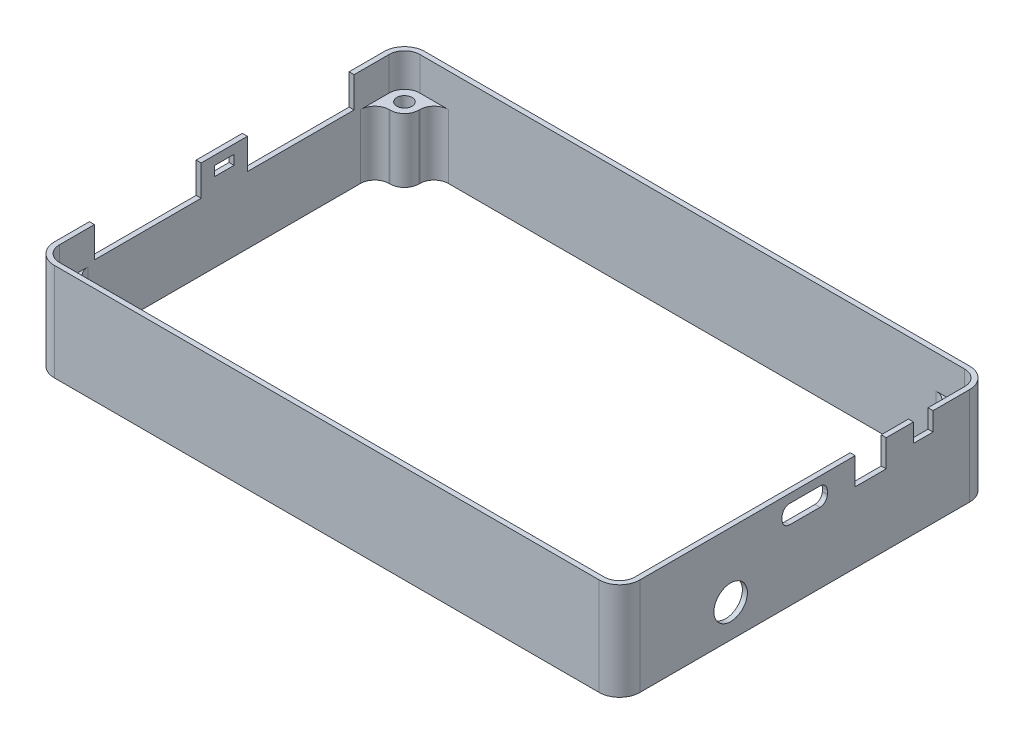
SolidWorks part; units mm, degrees
ref_plane "Front Plane" through (0, 0, 0) normal (0, 0, 1) x (1, 0, 0)
ref_plane "Top Plane" through (0, 0, 0) normal (0, 1, 0) x (1, 0, 0)
ref_plane "Right Plane" through (0, 0, 0) normal (1, 0, 0) x (0, 0, -1)
sketch "pcb" plane through (0, 0, 0) normal (0, 1, 0) x (1, 0, 0)
  line L0 (-14, -27.5) -> (-42, -27.5) construction
  line L1 (-57, -37.5) -> (57, -37.5)
  line L2 (-60, -34.5) -> (-60, 34.5)
  line L3 (-57, 37.5) -> (57, 37.5)
  line L4 (60, -34.5) -> (60, 34.5)
  line L5 (-60, -37.5) -> (60, 37.5) construction
  line L6 (-60, 37.5) -> (60, -37.5) construction
  line L7 (-14, -27.5) -> (14, -27.5) construction
  line L8 (14, -27.5) -> (42, -27.5) construction
  line L9 (-42, -27.5) -> (-60, -27.5) construction
  line L10 (42, -27.5) -> (60, -27.5) construction
  line L11 (-60, 0) -> (60, 0) construction
  line L13 (2.43, 12.5075) -> (10.05, 12.5075)
  line L14 (2.43, 12.5075) -> (2.43, 9.9675)
  line L15 (2.43, 9.9675) -> (10.05, 9.9675)
  line L16 (10.05, 12.5075) -> (10.05, 9.9675)
  arc A0 (-57, -37.5) -> (-60, -34.5) centre (-57, -34.5) cw
  arc A1 (57, -37.5) -> (60, -34.5) centre (57, -34.5) ccw
  arc A2 (57, 37.5) -> (60, 34.5) centre (57, 34.5) cw
  arc A3 (-60, 34.5) -> (-57, 37.5) centre (-57, 34.5) cw
  circle A4 centre (-57, 34.5) radius 1.6
  circle A5 centre (57, 34.5) radius 1.6
  circle A6 centre (57, -34.5) radius 1.6
  circle A7 centre (-57, -34.5) radius 1.6
  circle A8 centre (-42, -27.5) radius 5.5
  circle A9 centre (-14, -27.5) radius 5.5
  circle A10 centre (14, -27.5) radius 5.5
  circle A11 centre (42, -27.5) radius 5.5
  circle A12 centre (-42, 27.5) radius 5.5
  circle A13 centre (-14, 27.5) radius 5.5
  circle A14 centre (14, 27.5) radius 5.5
  circle A15 centre (42, 27.5) radius 5.5
  point P0 (0, 0)
  dimension "D3" = 3
  dimension "D4" = 3
  dimension "D5" = 3
  dimension "D6" = 3
  dimension "D7" = 3.2
  dimension "D9" = 11
  dimension "D10" = 18
  dimension "D1" = 120
  dimension "D2" = 75
  dimension "D8" = 10
  dimension "D11" = 62.43
  dimension "D12" = 47.4675
  dimension "D13" = 2.54
  dimension "D14" = 7.62
sketch "Sketch3" plane through (0, 0, 0) normal (0, 0, 1) x (1, 0, 0)
  line L0 (0, 0) -> (0, 1.6) construction
  line L1 (-57, 0) -> (57, 0) construction
  line L2 (0, 1.6) -> (0, 7) construction
  line L3 (0, 7) -> (0, 8.6) construction
  line L4 (0, 0) -> (0, -13.4) construction
  line L5 (0, -13.4) -> (0, -16.4) construction
  dimension "D1" = 1.6
  dimension "D2" = 3
  dimension "D3" = 13.4
  dimension "D4" = 5.4
  dimension "D5" = 1.6
  dimension "D6" = 25
sketch "Sketch2" plane through (0, 0, 0) normal (0, 1, 0) x (1, 0, 0)
  line L0 (-60, -34.5) -> (-60, 34.5) construction
  line L1 (-57, -37.5) -> (57, -37.5) construction
  line L2 (60, -34.5) -> (60, 34.5) construction
  line L3 (-57, 37.5) -> (57, 37.5) construction
  line L4 (-60, -34.5) -> (-60, 34.5)
  line L5 (-57, -37.5) -> (57, -37.5)
  line L6 (60, -34.5) -> (60, 34.5)
  line L7 (-57, 37.5) -> (57, 37.5)
  line L8 (-61.25, -34.5) -> (-61.25, 34.5)
  line L9 (-57, -38.75) -> (57, -38.75)
  line L10 (61.25, -34.5) -> (61.25, 34.5)
  line L11 (-57, 38.75) -> (57, 38.75)
  arc A0 (-57, 37.5) -> (-60, 34.5) centre (-57, 34.5) ccw construction
  arc A1 (-60, -34.5) -> (-57, -37.5) centre (-57, -34.5) ccw construction
  arc A2 (57, -37.5) -> (60, -34.5) centre (57, -34.5) ccw construction
  arc A3 (60, 34.5) -> (57, 37.5) centre (57, 34.5) ccw construction
  arc A4 (-57, 37.5) -> (-60, 34.5) centre (-57, 34.5) ccw
  arc A5 (-60, -34.5) -> (-57, -37.5) centre (-57, -34.5) ccw
  arc A6 (57, -37.5) -> (60, -34.5) centre (57, -34.5) ccw
  arc A7 (60, 34.5) -> (57, 37.5) centre (57, 34.5) ccw
  arc A8 (-57, 38.75) -> (-61.25, 34.5) centre (-57, 34.5) ccw
  arc A9 (-61.25, -34.5) -> (-57, -38.75) centre (-57, -34.5) ccw
  arc A10 (57, -38.75) -> (61.25, -34.5) centre (57, -34.5) ccw
  arc A11 (61.25, 34.5) -> (57, 38.75) centre (57, 34.5) ccw
  dimension "D1" = 1.25
extrude "Walls" add sketch "Sketch2" against normal up to vertex (13.4 mm away) and the other way up to vertex (7 mm away) up to point (0, -13.4, 0) other way up to point (0, 7, 0)
sketch "Sketch11" plane through (0, 0, 0) normal (0, 1, 0) x (1, 0, 0)
  line L0 (-60, -34.5) -> (-60, -31.5)
  line L1 (-60, -34.5) -> (-60, 34.5) construction
  line L2 (-60, -31.5) -> (-54, -31.5)
  line L3 (-54, -31.5) -> (-54, -37.5)
  line L4 (-57, -37.5) -> (57, -37.5) construction
  line L5 (-54, -37.5) -> (-57, -37.5)
  line L6 (-57, 37.5) -> (-54, 37.5)
  line L7 (-57, 37.5) -> (57, 37.5) construction
  line L8 (-54, 37.5) -> (-54, 31.5)
  line L9 (-54, 31.5) -> (-60, 31.5)
  line L10 (-60, 31.5) -> (-60, 34.5)
  line L11 (60, -31.5) -> (54, -31.5)
  line L12 (60, -34.5) -> (60, 34.5) construction
  line L13 (54, -31.5) -> (54, -37.5)
  line L14 (54, -37.5) -> (57, -37.5)
  line L15 (60, -31.5) -> (60, -34.5)
  line L16 (57, 37.5) -> (54, 37.5)
  line L17 (54, 37.5) -> (54, 31.5)
  line L18 (54, 31.5) -> (60, 31.5)
  line L19 (60, 31.5) -> (60, 34.5)
  arc A0 (-60, -34.5) -> (-57, -37.5) centre (-57, -34.5) ccw construction
  arc A1 (-60, -34.5) -> (-57, -37.5) centre (-57, -34.5) ccw
  arc A2 (-57, 37.5) -> (-60, 34.5) centre (-57, 34.5) ccw construction
  arc A3 (-57, 37.5) -> (-60, 34.5) centre (-57, 34.5) ccw
  circle A4 centre (-57, 34.5) radius 1.6 construction
  circle A5 centre (-57, 34.5) radius 1.6
  circle A6 centre (-57, -34.5) radius 1.6 construction
  circle A7 centre (-57, -34.5) radius 1.6
  arc A8 (57, -37.5) -> (60, -34.5) centre (57, -34.5) ccw construction
  arc A9 (57, -37.5) -> (60, -34.5) centre (57, -34.5) ccw
  circle A10 centre (57, -34.5) radius 1.6 construction
  circle A11 centre (57, -34.5) radius 1.6
  arc A12 (60, 34.5) -> (57, 37.5) centre (57, 34.5) ccw construction
  arc A13 (60, 34.5) -> (57, 37.5) centre (57, 34.5) ccw
  circle A14 centre (57, 34.5) radius 1.6 construction
  circle A15 centre (57, 34.5) radius 1.6
  dimension "D1" = 6
  dimension "D2" = 6
  dimension "D3" = 6
  dimension "D4" = 6
extrude "Boss-Extrude4" add sketch "Sketch11" against normal up to surface (13.4 mm away) up to face at (0, -13.4, 0)
other "Move Face7" face at (58.8107, 3.5, 36.3107) face at (60, -1.6, 0) face at (58.8107, 3.5, -36.3107) face at (0, -1.6, -37.5) face at (-58.8107, 3.5, -36.3107) face at (-60, -1.6, 0) face at (0, -1.6, 37.5) face at (-58.8107, 3.5, 36.3107) parameters "D1"=0.2
fillet "Fillet1" radius 3 12 edges at (60.2, -6.7, -31.5) (54, -6.7, -37.7) (-54, -6.7, -37.7) (-60.2, -6.7, -31.5) (-54, -6.7, 37.7) (-60.2, -6.7, 31.5) (54, -6.7, 37.7) (60.2, -6.7, 31.5) (54, -6.7, 31.5) (-54, -6.7, 31.5) (-54, -6.7, -31.5) (54, -6.7, -31.5)
sketch "Sketch8" plane through (61.25, 0, 0) normal (1, 0, 0) x (0, 0, -1)
  line L0 (0, 1.6) -> (0, 7) construction
  line L1 (-3.17, 1.57) -> (3.17, 1.57)
  line L2 (-4.47, 2.87) -> (-4.47, 3.63)
  line L3 (-3.17, 4.93) -> (3.17, 4.93)
  line L4 (4.47, 2.87) -> (4.47, 3.63)
  line L5 (-4.47, 1.57) -> (4.47, 4.93) construction
  line L6 (-4.47, 4.93) -> (4.47, 1.57) construction
  line L7 (23, 4.87) -> (23, 7)
  line L8 (0, 0) -> (0, 1.6) construction
  line L9 (0, 0) -> (0, 1.6) construction
  line L10 (-34.5, 7) -> (34.5, 7) construction
  line L11 (16.8, 1.6) -> (10.8, 1.6)
  line L12 (16.8, 1.6) -> (16.8, 6.82)
  line L13 (16.8, 6.82) -> (10.8, 6.82)
  line L14 (10.8, 1.6) -> (10.8, 6.82)
  line L15 (-37.5, 0) -> (37.5, 0) construction
  line L16 (0, 0) -> (0, -13.4) construction
  line L17 (23, 7) -> (26.6, 7)
  line L18 (23, 4.87) -> (26.6, 4.87) construction
  line L19 (23, 4.87) -> (23, 3.37)
  line L20 (23, 3.37) -> (26.6, 3.37)
  line L21 (26.6, 4.87) -> (26.6, 3.37)
  line L22 (26.6, 7) -> (26.6, 4.87)
  arc A0 (3.17, 4.93) -> (4.47, 3.63) centre (3.17, 3.63) cw
  arc A1 (3.17, 1.57) -> (4.47, 2.87) centre (3.17, 2.87) ccw
  arc A2 (-3.17, 1.57) -> (-4.47, 2.87) centre (-3.17, 2.87) cw
  arc A3 (-4.47, 3.63) -> (-3.17, 4.93) centre (-3.17, 3.63) cw
  circle A4 centre (-15.5, -6.55) radius 3.25
  point P0 (0, 3.25)
  point P10 (13.8, 1.6)
  dimension "D4" = 1.3
  dimension "D5" = 1.3
  dimension "D6" = 1.3
  dimension "D7" = 1.3
  dimension "D11" = 6.5
  dimension "D1" = 3.36
  dimension "D2" = 8.94
  dimension "D3" = 3.25
  dimension "D8" = 13.8
  dimension "D9" = 6
  dimension "D10" = 5.22
  dimension "D12" = 6.55
  dimension "D13" = 15.5
  dimension "D14" = 1.5
  dimension "D15" = 3.6
  dimension "D16" = 1.77
  dimension "D17" = 9.2
extrude "Cut-Extrude3" cut sketch "Sketch8" along direction (1, 0, 0) on the side against the normal up to surface (1.05 mm away)
sketch "Sketch10" plane through (-61.25, 0, 0) normal (-1, 0, 0) x (0, 0, 1)
  line L0 (-34.5, 7) -> (34.5, 7) construction
  line L1 (5.84, 1.6) -> (26.16, 1.6)
  line L2 (5.84, 1.6) -> (5.84, 7)
  line L3 (5.84, 7) -> (26.16, 7)
  line L4 (26.16, 1.6) -> (26.16, 7)
  line L6 (-5.84, 1.6) -> (-26.16, 1.6)
  line L7 (-5.84, 1.6) -> (-5.84, 7)
  line L8 (-5.84, 7) -> (-26.16, 7)
  line L9 (-26.16, 1.6) -> (-26.16, 7)
  line L10 (0, 0) -> (0, 1.6) construction
  line L15 (0, 0) -> (0, 1.6) construction
  line L16 (-5.84, 1.6) -> (0, 1.6) construction
  line L17 (0, 1.6) -> (5.84, 1.6) construction
  line L22 (-1.8, 4.87) -> (1.8, 4.87)
  line L23 (-1.8, 4.87) -> (-1.8, 3.37)
  line L24 (-1.8, 3.37) -> (1.8, 3.37)
  line L25 (1.8, 4.87) -> (1.8, 3.37)
  point P10 (0, 3.37)
  dimension "D1" = 20.32
  dimension "D2" = 20.32
  dimension "D3" = 11.68
  dimension "D4" = 3.6
  dimension "D5" = 1.5
  dimension "D6" = 1.77
extrude "Cut-Extrude4" cut sketch "Sketch10" against normal up to next
other "Move Face3" face at (60.725, 5.185, -23) face at (60.725, 5.185, -26.6) face at (60.725, 3.37, -24.8) parameters "D1"=0.25
other "Move Face4" face at (60.2, -6.55, 12.25) face at (60.725, 2.0854, 3.9546) face at (60.725, 3.25, 4.47) face at (60.725, 4.4146, 3.9546) face at (60.725, 4.93, 0) face at (60.725, 2.0854, -3.9546) face at (60.725, 1.57, 0) face at (60.725, 3.25, -4.47) face at (60.725, 4.4146, -3.9546) face at (60.725, 1.6, -13.8) face at (60.725, 4.21, -16.8) face at (60.725, 4.21, -10.8) face at (60.725, 6.82, -13.8) parameters "D1"=0.25
other "Move Face1" face at (-60.725, 4.3, 26.16) face at (-60.725, 1.6, 16) face at (-60.725, 4.3, 5.84) face at (-60.725, 4.3, -26.16) face at (-60.725, 1.6, -16) face at (-60.725, 4.3, -5.84) parameters "D1"=1
other "Move Face2" face at (-60.725, 4.12, -1.8) face at (-60.725, 4.87, 0) face at (-60.725, 3.37, 0) face at (-60.725, 4.12, 1.8) parameters "D1"=0.25
sketch "Sketch4" plane through (0, -13.4, 0) normal (0, -1, 0) x (1, 0, 0)
  line L4 (-57, -38.75) -> (57, -38.75)
  line L5 (61.25, -34.5) -> (61.25, 34.5)
  line L6 (57, 38.75) -> (-57, 38.75)
  line L7 (-61.25, 34.5) -> (-61.25, -34.5)
  line L8 (-57, -38.75) -> (57, -38.75)
  line L9 (61.25, -34.5) -> (61.25, 34.5)
  line L10 (57, 38.75) -> (-57, 38.75)
  line L11 (-61.25, 34.5) -> (-61.25, -34.5)
  circle A0 centre (57, -34.5) radius 2.15
  circle A1 centre (-57, -34.5) radius 2.15
  circle A2 centre (-57, 34.5) radius 2.15
  circle A3 centre (57, 34.5) radius 2.15
  arc A4 (-61.25, -34.5) -> (-57, -38.75) centre (-57, -34.5) ccw
  arc A5 (57, -38.75) -> (61.25, -34.5) centre (57, -34.5) ccw
  arc A6 (61.25, 34.5) -> (57, 38.75) centre (57, 34.5) ccw
  arc A7 (-57, 38.75) -> (-61.25, 34.5) centre (-57, 34.5) ccw
  arc A8 (-61.25, -34.5) -> (-57, -38.75) centre (-57, -34.5) ccw
  arc A9 (57, -38.75) -> (61.25, -34.5) centre (57, -34.5) ccw
  arc A10 (61.25, 34.5) -> (57, 38.75) centre (57, 34.5) ccw
  arc A11 (-57, 38.75) -> (-61.25, 34.5) centre (-57, 34.5) ccw
  dimension "D2" = 4.3
  dimension "D1" = 0
extrude "Bottom Lid" add sketch "Sketch4" along normal blind 3 separate body
sketch "Sketch5" plane through (0, 7, 0) normal (0, 1, 0) x (1, 0, 0)
  line L0 (2.43, 12.5075) -> (2.43, 9.9675) construction
  line L1 (2.43, 9.9675) -> (10.05, 9.9675) construction
  line L2 (2.43, 12.5075) -> (10.05, 12.5075) construction
  line L3 (10.05, 12.5075) -> (10.05, 9.9675) construction
  line L4 (57, 38.75) -> (-57, 38.75)
  line L5 (61.25, -34.5) -> (61.25, 34.5)
  line L6 (-57, -38.75) -> (57, -38.75)
  line L7 (-61.25, 34.5) -> (-61.25, -34.5)
  line L12 (57, 38.75) -> (-57, 38.75)
  line L13 (61.25, -34.5) -> (61.25, 34.5)
  line L14 (-57, -38.75) -> (57, -38.75)
  line L15 (-61.25, 34.5) -> (-61.25, -34.5)
  line L16 (2.43, 12.5075) -> (2.43, 9.9675)
  line L17 (2.43, 9.9675) -> (10.05, 9.9675)
  line L18 (2.43, 12.5075) -> (10.05, 12.5075)
  line L19 (10.05, 12.5075) -> (10.05, 9.9675)
  circle A3 centre (42, 27.5) radius 5.5 construction
  circle A15 centre (42, 27.5) radius 5.5
  circle A16 centre (-14, 27.5) radius 5.5 construction
  circle A17 centre (14, 27.5) radius 5.5 construction
  circle A18 centre (-14, 27.5) radius 5.5
  circle A19 centre (14, 27.5) radius 5.5
  circle A20 centre (-42, 27.5) radius 5.5 construction
  circle A21 centre (-42, 27.5) radius 5.5
  circle A22 centre (42, -27.5) radius 5.5 construction
  circle A23 centre (14, -27.5) radius 5.5 construction
  circle A24 centre (-14, -27.5) radius 5.5 construction
  circle A25 centre (-42, -27.5) radius 5.5 construction
  circle A26 centre (42, -27.5) radius 5.5
  circle A27 centre (14, -27.5) radius 5.5
  circle A28 centre (-14, -27.5) radius 5.5
  circle A29 centre (-42, -27.5) radius 5.5
  circle A30 centre (-57, -34.5) radius 1.6 construction
  circle A31 centre (-57, 34.5) radius 1.6 construction
  circle A32 centre (57, 34.5) radius 1.6 construction
  circle A33 centre (57, -34.5) radius 1.6 construction
  circle A34 centre (-57, -34.5) radius 1.6
  circle A35 centre (-57, 34.5) radius 1.6
  circle A36 centre (57, 34.5) radius 1.6
  circle A37 centre (57, -34.5) radius 1.6
  arc A38 (-57, 38.75) -> (-61.25, 34.5) centre (-57, 34.5) ccw
  arc A39 (61.25, 34.5) -> (57, 38.75) centre (57, 34.5) ccw
  arc A40 (57, -38.75) -> (61.25, -34.5) centre (57, -34.5) ccw
  arc A41 (-61.25, -34.5) -> (-57, -38.75) centre (-57, -34.5) ccw
  arc A42 (-57, 38.75) -> (-61.25, 34.5) centre (-57, 34.5) ccw
  arc A43 (61.25, 34.5) -> (57, 38.75) centre (57, 34.5) ccw
  arc A44 (57, -38.75) -> (61.25, -34.5) centre (57, -34.5) ccw
  arc A45 (-61.25, -34.5) -> (-57, -38.75) centre (-57, -34.5) ccw
  dimension "D1" = 0
extrude "Top Lid" add sketch "Sketch5" along normal blind 1.6 separate body
other "Move Face5" face at (2.43, 7.8, -11.2375) face at (6.24, 7.8, -9.9675) face at (10.05, 7.8, -11.2375) face at (6.24, 7.8, -12.5075) parameters "D1"=0.25
delete or keep bodies "Body-Delete/Keep 1" type keep bodies bodies 120
delete or keep bodies "Body-Delete/Keep 2" [suppressed] type keep bodies bodies 124
delete or keep bodies "Body-Delete/Keep 3" [suppressed] type keep bodies bodies 102
other "Top Lid Offset" [suppressed] parameters "D1"=0.0762
other "Top Lid Offset 2" [suppressed] parameters "D1"=0.1
other "Move Face6" [suppressed] parameters "D1"=0.0762
equation "\"D2@Sketch10\"=\"D1@Sketch10\""
equation "\"D2@Sketch11\"=\"D1@Sketch11\""
equation "\"D3@Sketch11\"=\"D1@Sketch11\""
equation "\"D4@Sketch11\"=\"D1@Sketch11\""
